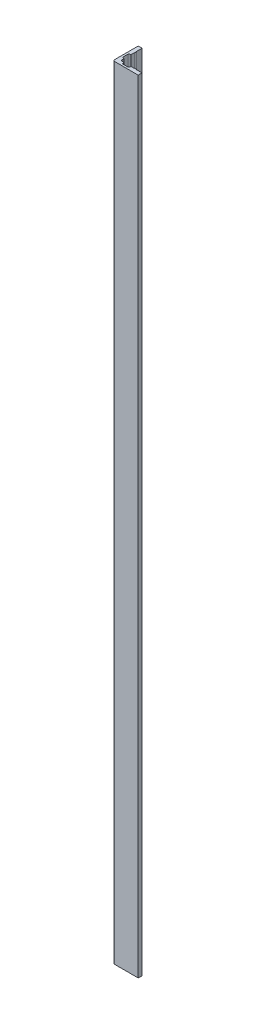
SolidWorks part; units mm, degrees
ref_plane "Front Plane" through (0, 0, 0) normal (0, 0, 1) x (1, 0, 0)
ref_plane "Top Plane" through (0, 0, 0) normal (0, 1, 0) x (1, 0, 0)
ref_plane "Right Plane" through (0, 0, 0) normal (1, 0, 0) x (0, 0, -1)
sketch "Sketch2" plane through (0, 0, 0) normal (0, 1, 0) x (1, 0, 0)
  line L0 (0, 0) -> (50, 0)
  line L1 (50, 0) -> (50, -9)
  line L2 (50, -9) -> (-9, -9)
  line L3 (-9, -9) -> (-9, 50)
  line L4 (-9, 50) -> (0, 50)
  line L5 (0, 50) -> (0, 0)
  dimension "D1" = 50
  dimension "D2" = 50
  dimension "D3" = 9
  dimension "D4" = 9
extrude "Boss-Extrude1" add sketch "Sketch2" along normal blind 1828.8
sketch "Sketch6" plane through (0, 1828.8, 0) normal (0, 1, 0) x (1, 0, 0)
  line L0 (0, 0) -> (0, 31.75) construction
  line L1 (0, 0) -> (0, 50) construction
  line L3 (0, 31.75) -> (1, 31.75)
  line L4 (0, 31.75) -> (0, 35.75)
  line L5 (0, 35.75) -> (1, 35.75)
  line L6 (1, 31.75) -> (1, 35.75)
  dimension "D1" = 31.75
  dimension "D2" = 1
  dimension "D3" = 4
extrude "Boss-Extrude2" add sketch "Sketch6" against normal through all
sketch "Sketch7" plane through (0, 1828.8, 0) normal (0, 1, 0) x (1, 0, 0)
  line L0 (0, 0) -> (31.75, 0) construction
  line L2 (31.75, 0) -> (35.75, 0)
  line L3 (31.75, 0) -> (31.75, 1)
  line L4 (31.75, 1) -> (35.75, 1)
  line L5 (35.75, 0) -> (35.75, 1)
  dimension "D1" = 31.75
  dimension "D2" = 1
  dimension "D3" = 4
extrude "Boss-Extrude3" add sketch "Sketch7" against normal through all
sketch "Sketch8" plane through (0, 1828.8, 0) normal (0, 1, 0) x (1, 0, 0)
  line L0 (31.75, 0) -> (0, 0) construction
  line L1 (8, 0) -> (23.75, 0)
  line L2 (8, 0) -> (8, -4.5)
  line L3 (8, -4.5) -> (23.75, -4.5)
  line L4 (23.75, 0) -> (23.75, -4.5)
  line L5 (0, 0) -> (0, 31.75) construction
  line L6 (31.75, 1) -> (31.75, 0) construction
  dimension "D1" = 8
  dimension "D2" = 8
  dimension "D3" = 4.5
extrude "Cut-Extrude3" cut sketch "Sketch8" against normal through all
sketch "Sketch9" plane through (0, 1828.8, 0) normal (0, 1, 0) x (1, 0, 0)
  line L0 (0, 0) -> (0, 31.75) construction
  line L1 (0, 8) -> (-4.5, 8)
  line L2 (0, 8) -> (0, 23.75)
  line L3 (0, 23.75) -> (-4.5, 23.75)
  line L4 (-4.5, 8) -> (-4.5, 23.75)
  line L5 (8, 0) -> (0, 0) construction
  line L6 (0, 31.75) -> (1, 31.75) construction
  dimension "D1" = 8
  dimension "D2" = 8
  dimension "D3" = 4.5
extrude "Cut-Extrude4" cut sketch "Sketch9" against normal through all
fillet "Fillet4" radius 2 4 edges at (23.75, 914.4, 4.5) (8, 914.4, 4.5) (-4.5, 914.4, -8) (-4.5, 914.4, -23.75)
fillet "Fillet2" radius 3.66 1 edges at (0, 914.4, 0)
fillet "Fillet3" radius 3.66 1 edges at (-9, 914.4, 9)
